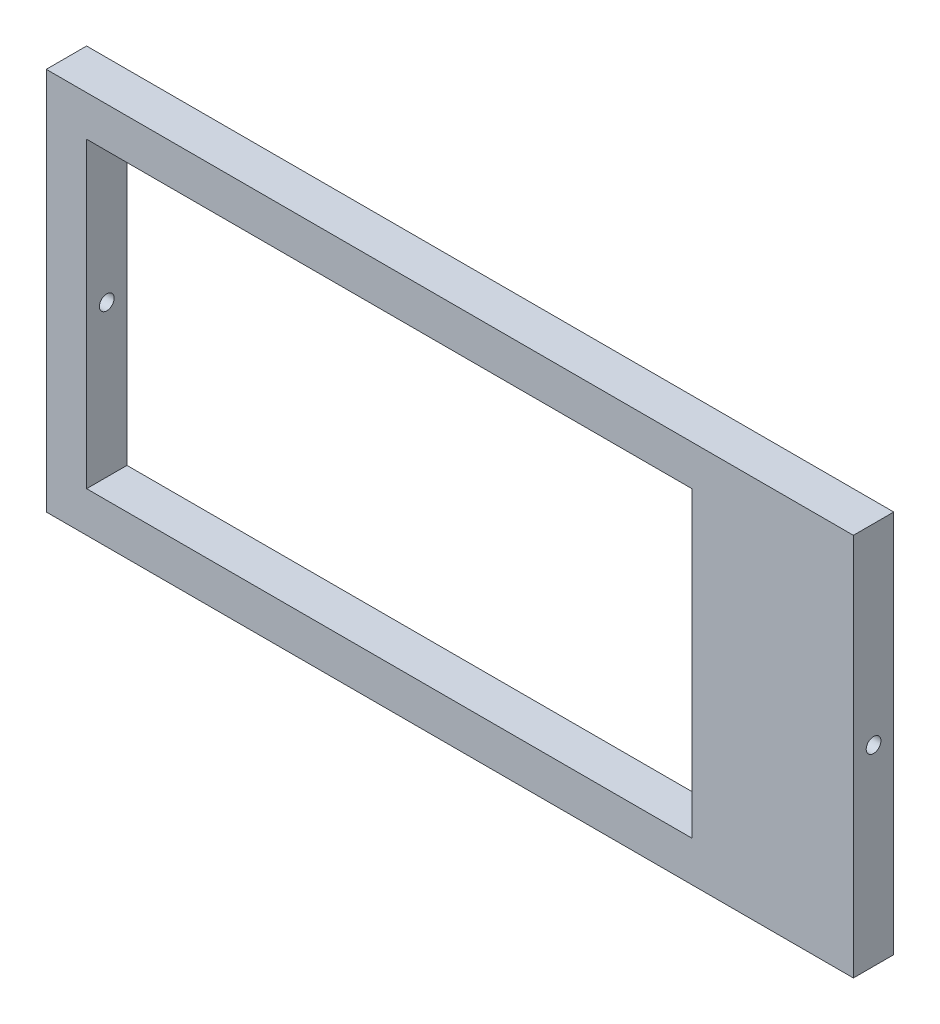
SolidWorks part; units mm, degrees
ref_plane "Front Plane" through (0, 0, 0) normal (0, 0, 1) x (1, 0, 0)
ref_plane "Top Plane" through (0, 0, 0) normal (0, 1, 0) x (1, 0, 0)
ref_plane "Right Plane" through (0, 0, 0) normal (1, 0, 0) x (0, 0, -1)
sketch "Sketch1" plane through (0, 0, 0) normal (0, 0, 1) x (1, 0, 0)
  line L1 (0, 0) -> (40, 0)
  line L2 (0, 0) -> (0, 19)
  line L3 (0, 19) -> (40, 19)
  line L4 (40, 0) -> (40, 19)
  line L5 (2, 17) -> (32, 17)
  line L6 (2, 17) -> (2, 2)
  line L7 (2, 2) -> (32, 2)
  line L8 (32, 17) -> (32, 2)
  dimension "D1" = 40
  dimension "D2" = 19
  dimension "D3" = 30
  dimension "D4" = 15
  dimension "D5" = 2
  dimension "D6" = 2
extrude "Boss-Extrude1" add sketch "Sketch1" along normal blind 2
sketch "Sketch2" plane through (40, 0, 0) normal (1, 0, 0) x (0, 0, -1)
  circle A0 centre (-1, 9.5) radius 0.365
extrude "Cut-Extrude1" cut sketch "Sketch2" against normal through all
